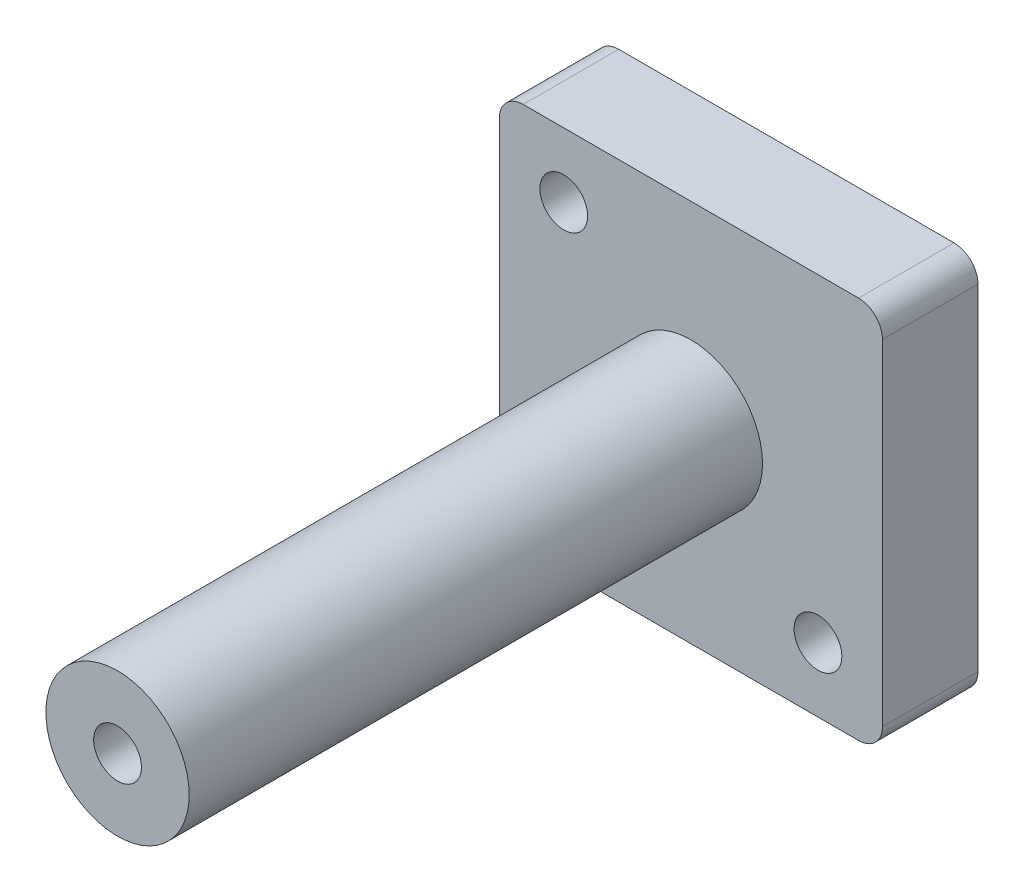
SolidWorks part; units mm, degrees
ref_plane "Front Plane" through (0, 0, 0) normal (0, 0, 1) x (1, 0, 0)
ref_plane "Top Plane" through (0, 0, 0) normal (0, 1, 0) x (1, 0, 0)
ref_plane "Right Plane" through (0, 0, 0) normal (1, 0, 0) x (0, 0, -1)
sketch "Sketch1" plane through (0, 0, 0) normal (0, 0, 1) x (1, 0, 0)
  line L1 (2.5, 0) -> (37.6, 0)
  line L2 (0, 2.5) -> (0, 37.6)
  line L3 (2.5, 40.1) -> (37.6, 40.1)
  line L4 (40.1, 2.5) -> (40.1, 37.6)
  circle A0 centre (6.75, 33.35) radius 2.5
  circle A1 centre (33.35, 6.75) radius 2.5
  arc A2 (2.5, 0) -> (0, 2.5) centre (2.5, 2.5) cw
  arc A3 (37.6, 0) -> (40.1, 2.5) centre (37.6, 2.5) ccw
  arc A4 (37.6, 40.1) -> (40.1, 37.6) centre (37.6, 37.6) cw
  arc A5 (0, 37.6) -> (2.5, 40.1) centre (2.5, 37.6) cw
  point P9 (0, 0)
  point P11 (8.9793, 29.2244)
  point P16 (0, 0)
  point P21 (40.1, 40.1)
  point P24 (0, 40.1)
  dimension "D2" = 5
  dimension "D7" = 2.5
  dimension "D1" = 40.1
  dimension "D3" = 6.75
  dimension "D4" = 6.75
  dimension "D5" = 6.75
  dimension "D6" = 6.75
extrude "Boss-Extrude1" add sketch "Sketch1" along normal blind 10
sketch "Sketch2" plane through (0, 0, 10) normal (0, 0, 1) x (1, 0, 0)
  line L0 (0, 37.6) -> (0, 2.5) construction
  line L1 (37.6, 40.1) -> (2.5, 40.1) construction
  circle A0 centre (20.05, 20.05) radius 7.5
  point P4 (0, 20.05)
  point P8 (20.05, 40.1)
  dimension "D1" = 15
extrude "Boss-Extrude2" add sketch "Sketch2" along normal blind 60
sketch "Sketch3" plane through (0, 0, 70) normal (0, 0, 1) x (1, 0, 0)
  circle A0 centre (20.05, 20.05) radius 2.5
  dimension "D1" = 5
extrude "Cut-Extrude1" cut sketch "Sketch3" against normal blind 15
